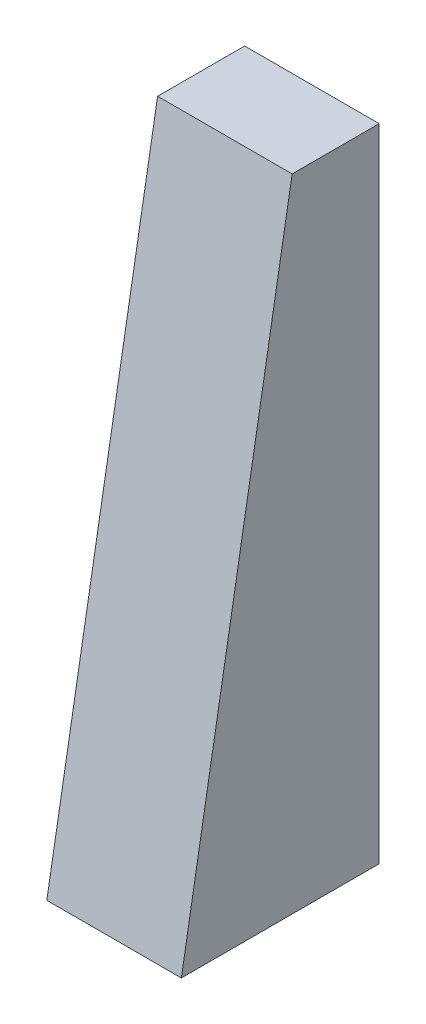
SolidWorks part; units mm, degrees
ref_plane "Front Plane" through (0, 0, 0) normal (0, 0, 1) x (1, 0, 0)
ref_plane "Top Plane" through (0, 0, 0) normal (0, 1, 0) x (1, 0, 0)
ref_plane "Right Plane" through (0, 0, 0) normal (1, 0, 0) x (0, 0, -1)
sketch "Sketch1" plane through (0, 0, 0) normal (1, 0, 0) x (0, 0, -1)
  line L0 (0, 0) -> (0, 810)
  line L1 (0, 810) -> (-110, 810)
  line L2 (-110, 810) -> (-250, 0)
  line L3 (-250, 0) -> (0, 0)
  point P3 (-171.3261, 810)
  dimension "D1" = 810
  dimension "D2" = 250
  dimension "D3" = 110
extrude "Boss-Extrude1" add sketch "Sketch1" along normal blind 170
